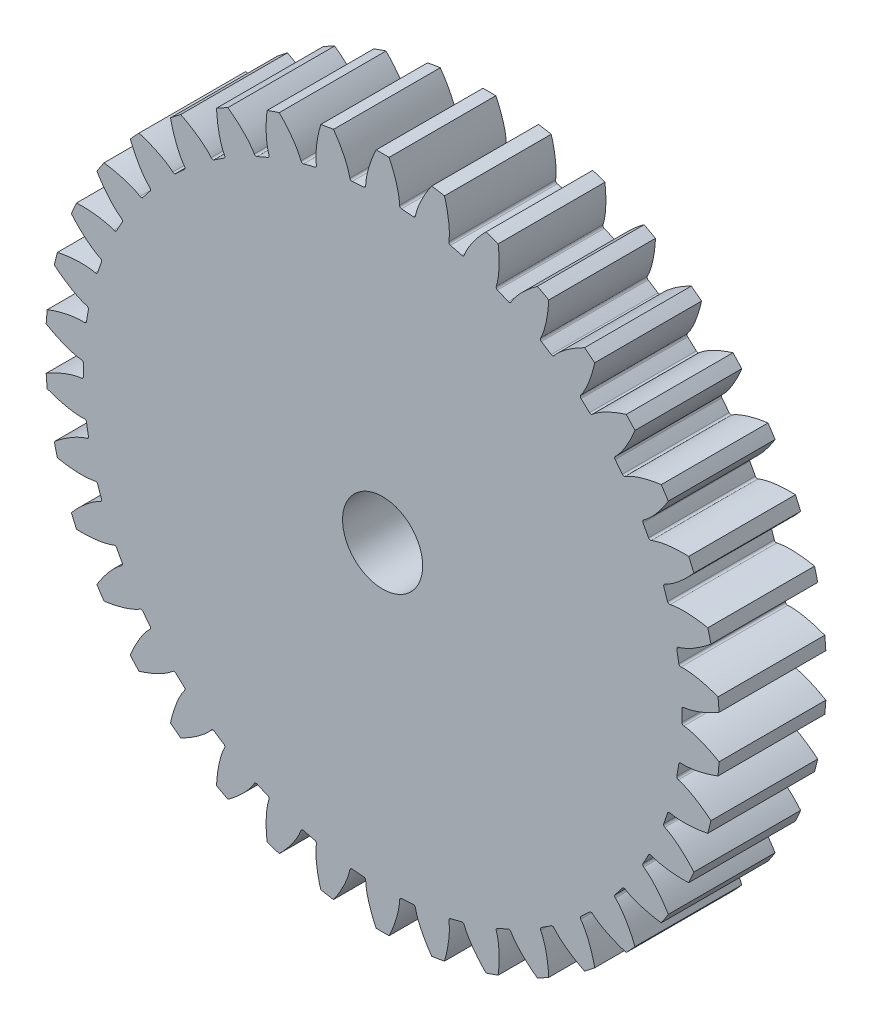
SolidWorks part; units mm, degrees
ref_plane "Front Plane" through (0, 0, 0) normal (0, 0, 1) x (1, 0, 0)
ref_plane "Top Plane" through (0, 0, 0) normal (0, 1, 0) x (1, 0, 0)
ref_plane "Right Plane" through (0, 0, 0) normal (1, 0, 0) x (0, 0, -1)
sketch "D" plane through (0, 0, 0) normal (0, 0, 1) x (1, 0, 0)
  circle A0 centre (0, 0) radius 12 construction
  dimension "D1" = 24
sketch "De, Di, Db" plane through (0, 0, 0) normal (0, 0, 1) x (1, 0, 0)
  circle A0 centre (0, 0) radius 11.2763 construction
  circle A1 centre (0, 0) radius 12.63 construction
  circle A2 centre (0, 0) radius 11.2125 construction
  point P7 (0, 0)
  dimension "D1" = 22.5526
  dimension "D2" = 25.26
  dimension "D3" = 22.425
sketch "Sketch4" plane through (0, 0, 0) normal (0, 0, 1) x (1, 0, 0)
  circle A0 centre (0, 0) radius 12.63 construction
  circle A1 centre (0, 0) radius 12.63
extrude "Addendum Extruded" add sketch "Sketch4" along normal mid plane 4
sketch "Tooth Profile Curve" plane through (0, 0, 0) normal (0, 0, 1) x (1, 0, 0)
  line L0 (0, 0) -> (12.63, 0) construction
  line L1 (0, 0) -> (11.2724, 0.2976) construction
  line L2 (0, 0) -> (11.9898, 0.4947) construction
  line L3 (11.2724, 0.2976) -> (11.2086, 0.296)
  line L4 (11.2125, 0) -> (12.63, 0)
  circle A0 centre (0, 0) radius 11.2763 construction
  circle A1 centre (0, 0) radius 12.63 construction
  circle A2 centre (0, 0) radius 11.2125 construction
  circle A3 centre (0, 0) radius 12 construction
  arc A4 (11.2086, 0.296) -> (11.2125, 0) centre (0, 0) cw
  arc A5 (12.63, 0) -> (12.6045, 0.8018) centre (0, 0) ccw
  spline S0 degree 4 poles (11.2724, 0.2976) (11.2807, 0.298) (11.304, 0.2997) (11.348, 0.3049) (11.4193, 0.3165) (11.5096, 0.3357) (11.6252, 0.3656) (11.76, 0.4073) (11.9063, 0.4598) (12.0633, 0.5241) (12.2177, 0.5945) (12.3696, 0.6705) (12.5188, 0.7513) (12.6969, 0.8551) (12.9066, 0.9878) (13.1456, 1.1546) (13.4091, 1.3574) (13.669, 1.578) (13.9172, 1.8065) (14.159, 2.0499) (14.3863, 2.2942) (14.6124, 2.5601) (14.8161, 2.8118) (15.0324, 3.1066) (15.2037, 3.3482) (15.4165, 3.6798) (15.5382, 3.8794) (15.676, 4.1173) (15.7347, 4.2251) (15.7709, 4.2915) knots 0 0 0 0 0 0.005377 0.015084 0.028532 0.04661 0.064855 0.092111 0.119476 0.146842 0.174209 0.201575 0.228941 0.256307 0.307035 0.361767 0.4165 0.471232 0.525964 0.580697 0.635429 0.690161 0.744894 0.799626 0.854358 0.909091 0.954545 1 1 1 1 1 construction
  spline S1 degree 4 poles (11.2724, 0.2976) (11.2807, 0.298) (11.304, 0.2997) (11.348, 0.3049) (11.4193, 0.3165) (11.5096, 0.3357) (11.6252, 0.3656) (11.76, 0.4073) (11.9063, 0.4598) (12.0633, 0.5241) (12.2177, 0.5945) (12.3696, 0.6705) (12.5188, 0.7513) (12.6969, 0.8551) (12.9066, 0.9878) (13.1456, 1.1546) (13.4091, 1.3574) (13.669, 1.578) (13.9172, 1.8065) (14.159, 2.0499) (14.3863, 2.2942) (14.6124, 2.5601) (14.8161, 2.8118) (15.0324, 3.1066) (15.2037, 3.3482) (15.3703, 3.6079) (15.4499, 3.7358) (15.4899, 3.8017) knots 0 0 0 0 0 0.005377 0.015084 0.028532 0.04661 0.064855 0.092111 0.119476 0.146842 0.174209 0.201575 0.228941 0.256307 0.307035 0.361767 0.4165 0.471232 0.525964 0.580697 0.635429 0.690161 0.744894 0.799626 0.854358 0.909091 0.909091 0.909091 0.909091 0.909091
  dimension "D1" = 2.363
  dimension "D2" = 0.85
  dimension "D3" = 1.513
extrude "1/2 Tooth Cut" cut sketch "Tooth Profile Curve" against normal mid plane 4
ref_plane "Plane of Mirroring" through (0, 0, 0) normal (0, 1, 0) x (1, 0, 0)
mirror "Mirror Tooth Cut" about plane through (0, 0, 0) normal (0, 1, 0) of "1/2 Tooth Cut"
fillet "Roots Fillet" radius 0.0788 2 edges at (11.2086, -0.296, 0) (11.2086, 0.296, 0)
pattern_circular "Circular Pattern of Teeth" count 38 over 360 about axis through (0, 0, -2) along (0, 0, 1) of "Mirror Tooth Cut", "1/2 Tooth Cut", "Roots Fillet"
sketch "Sketch5" plane through (0, 0, 0) normal (0, 0, 1) x (1, 0, 0)
  line L0 (1, 4) -> (-1, 4) construction
  line L1 (-1, 5) -> (1, 5)
  line L2 (-1, 5) -> (-1, 3.873)
  line L5 (1, 4) -> (1, 5)
  line L6 (1, 4) -> (1, 3.873)
  arc A0 (-1, 3.873) -> (1, 3.873) centre (0, 0) ccw
  circle A1 centre (0, 0) radius 4 construction
  point P9 (0, 5)
  dimension "D1" = 8
  dimension "D2" = 1
  dimension "D3" = 2
sketch "Sketch6" [suppressed] plane through (0, 0, 0) normal (0, 0, 1) x (1, 0, 0)
  line L6 (41.8591, 5.9947) -> (34.5048, 4.9415) construction
  line L7 (37.3883, 19.7543) -> (30.8195, 16.2837) construction
  line L8 (41.8591, 5.9947) -> (34.5048, 4.9415)
  line L9 (37.3883, 19.7543) -> (30.8195, 16.2837)
  arc A14 (52.1159, 14.1398) -> (50.4738, 19.1936) centre (0, 0) ccw construction
  arc A20 (34.5048, 4.9415) -> (33.5461, 3.7044) centre (34.6643, 3.8278) ccw construction
  arc A29 (29.3167, 16.721) -> (30.8195, 16.2837) centre (30.294, 17.2784) ccw construction
  circle A30 centre (0, 0) radius 33.75 construction
  arc A31 (52.1159, 14.1398) -> (50.4738, 19.1936) centre (0, 0) ccw
  arc A32 (34.5048, 4.9415) -> (33.5461, 3.7044) centre (34.6643, 3.8278) ccw
  arc A33 (29.3167, 16.721) -> (30.8195, 16.2837) centre (30.294, 17.2784) ccw
  arc A34 (29.3167, 16.721) -> (33.5461, 3.7044) centre (0, 0) ccw
  spline S2 degree 4 poles (965.1968, -1751.9554) (49.5722, -17.509) (34.0199, 17.1415) (35.6787, 19.1473) (37.9033, 19.963) (38.3849, 20.1134) (39.1305, 20.2925) (39.9677, 20.4275) (40.8649, 20.5145) (41.6597, 20.5534) (42.2962, 20.5635) (43.0686, 20.5519) (43.9989, 20.5031) (45.0849, 20.3985) (46.322, 20.2188) (47.5725, 19.978) (64.8653, 15.8708) (78.7396, -0.7897) (70.5074, -3.2513) (1756.2094, -1025.0114) knots -0.360808 -0.360808 -0.360808 -0.360808 -0.360808 0.005377 0.015084 0.028532 0.04661 0.092111 0.146842 0.174209 0.201575 0.228941 0.256307 0.307035 0.361767 0.4165 0.471232 0.525964 3.418372 3.418372 3.418372 3.418372 3.418372 only from (37.3883, 19.7543) to (50.4738, 19.1936) construction
  spline S3 degree 4 poles (-248.913, 1984.6901) (29.8132, 43.3029) (37.5982, 6.1286) (40.1192, 5.4809) (42.3983, 6.1286) (42.8764, 6.29) (43.5848, 6.5834) (44.3415, 6.9662) (45.1185, 7.4233) (45.7844, 7.859) (46.3053, 8.2249) (46.9233, 8.6882) (47.6473, 9.2745) (48.4644, 9.9975) (49.3596, 10.87) (50.2297, 11.7999) (61.8058, 25.2872) (63.2375, 46.9208) (55.1306, 44.0736) (818.3166, 1861.5256) knots -0.360808 -0.360808 -0.360808 -0.360808 -0.360808 0.005377 0.015084 0.028532 0.04661 0.092111 0.146842 0.174209 0.201575 0.228941 0.256307 0.307035 0.361767 0.4165 0.471232 0.525964 3.418372 3.418372 3.418372 3.418372 3.418372 only from (41.8591, 5.9947) to (52.1159, 14.1398) construction
  spline S4 degree 4 poles (37.3883, 19.7543) (37.4162, 19.7684) (37.4955, 19.8059) (37.6488, 19.8697) (37.9033, 19.963) (38.3849, 20.1134) (39.1305, 20.2925) (39.9677, 20.4275) (40.8649, 20.5145) (41.6597, 20.5534) (42.2962, 20.5635) (43.0686, 20.5519) (43.9989, 20.5031) (45.0849, 20.3985) (46.322, 20.2188) (47.5725, 19.978) (48.7682, 19.694) (49.6459, 19.4492) (50.2125, 19.2764) (50.4738, 19.1936) knots 0 0 0 0 0 0.005377 0.015084 0.028532 0.04661 0.092111 0.146842 0.174209 0.201575 0.228941 0.256307 0.307035 0.361767 0.4165 0.471232 0.525964 0.573123 0.573123 0.573123 0.573123 0.573123
  spline S5 degree 4 poles (41.8591, 5.9947) (41.8899, 5.9998) (41.9761, 6.016) (42.1376, 6.0545) (42.3983, 6.1286) (42.8764, 6.29) (43.5848, 6.5834) (44.3415, 6.9662) (45.1185, 7.4233) (45.7844, 7.859) (46.3053, 8.2249) (46.9233, 8.6882) (47.6473, 9.2745) (48.4644, 9.9975) (49.3596, 10.87) (50.2297, 11.7999) (51.0302, 12.7325) (51.5963, 13.4464) (51.9531, 13.9192) (52.1159, 14.1398) knots 0 0 0 0 0 0.005377 0.015084 0.028532 0.04661 0.092111 0.146842 0.174209 0.201575 0.228941 0.256307 0.307035 0.361767 0.4165 0.471232 0.525964 0.573123 0.573123 0.573123 0.573123 0.573123
extrude "Teeth Removing" [suppressed] cut sketch "Sketch6" against normal through all both flip side to cut
sketch "Sketch7" [suppressed] plane through (0, 0, 0) normal (0, 0, 1) x (1, 0, 0)
  line L0 (-3, 10) -> (3, 10)
  line L1 (3, 10) -> (3, 7.4162)
  line L2 (-3, 10) -> (-3, 7.4162)
  arc A0 (-3, 7.4162) -> (3, 7.4162) centre (0, 0) ccw
  point P1 (0, 10)
  dimension "D1" = 8
  dimension "D2" = 10
  dimension "D3" = 6
extrude "Cut-Extrude1" [suppressed] cut sketch "Sketch7" against normal through all both and the other way through all
sketch "Sketch8" [suppressed] plane through (0, 0, 0) normal (0, 0, 1) x (1, 0, 0)
  line L0 (-4.8226, 27.7752) -> (-3.9753, 22.8953) construction
  line L1 (4.8226, 27.7752) -> (3.9753, 22.8953) construction
  line L2 (-4.8226, 27.7752) -> (-3.9753, 22.8953)
  line L3 (4.8226, 27.7752) -> (3.9753, 22.8953)
  arc A0 (-4.5622, 22.0326) -> (4.5622, 22.0326) centre (0, 0) ccw
  arc A1 (-4.5622, 22.0326) -> (-3.9753, 22.8953) centre (-4.7142, 22.767) ccw construction
  arc A2 (3.9753, 22.8953) -> (4.5622, 22.0326) centre (4.7142, 22.767) ccw construction
  arc A3 (-4.5622, 22.0326) -> (-3.9753, 22.8953) centre (-4.7142, 22.767) ccw
  arc A4 (3.9753, 22.8953) -> (4.5622, 22.0326) centre (4.7142, 22.767) ccw
  arc A5 (-1.7713, 35.9564) -> (1.7713, 35.9564) centre (0, 0) cw
  spline S0 degree 4 poles (-2951.1447, 536.0596) (-42.0553, 30.3098) (3.4186, 24.472) (4.7778, 26.2412) (4.8488, 28.1447) (4.8449, 28.481) (4.8049, 28.9907) (4.718, 29.5493) (4.5883, 30.1361) (4.4492, 30.6481) (4.3245, 31.0537) (4.1581, 31.541) (3.9355, 32.1209) (3.6454, 32.7879) (3.2766, 33.5352) (2.8663, 34.2784) (-4.9345, 47.0779) (-24.4948, 52.3174) (-14.1166, 37.6796) (-2283.6828, 1979.2083) knots -0.444693 -0.444693 -0.444693 -0.444693 -0.444693 0.005377 0.015084 0.028532 0.04661 0.092111 0.146842 0.174209 0.201575 0.228941 0.256307 0.307035 0.361767 0.4165 0.471232 0.525964 4.228351 4.228351 4.228351 4.228351 4.228351 only from (4.8226, 27.7752) to (1.7713, 35.9564) construction
  spline S1 degree 4 poles (2951.1447, 536.0596) (42.0553, 30.3098) (-3.4186, 24.472) (-4.7778, 26.2412) (-4.8488, 28.1447) (-4.8449, 28.481) (-4.8049, 28.9907) (-4.718, 29.5493) (-4.5883, 30.1361) (-4.4492, 30.6481) (-4.3245, 31.0537) (-4.1581, 31.541) (-3.9355, 32.1209) (-3.6454, 32.7879) (-3.2766, 33.5352) (-2.8663, 34.2784) (4.9345, 47.0779) (24.4948, 52.3174) (14.1166, 37.6796) (2283.6828, 1979.2083) knots -0.444693 -0.444693 -0.444693 -0.444693 -0.444693 0.005377 0.015084 0.028532 0.04661 0.092111 0.146842 0.174209 0.201575 0.228941 0.256307 0.307035 0.361767 0.4165 0.471232 0.525964 4.228351 4.228351 4.228351 4.228351 4.228351 only from (-4.8226, 27.7752) to (-1.7713, 35.9564) construction
  spline S2 degree 4 poles (4.8226, 27.7752) (4.8257, 27.7958) (4.8332, 27.8538) (4.842, 27.9641) (4.8488, 28.1447) (4.8449, 28.481) (4.8049, 28.9907) (4.718, 29.5493) (4.5883, 30.1361) (4.4492, 30.6481) (4.3245, 31.0537) (4.1581, 31.541) (3.9355, 32.1209) (3.6454, 32.7879) (3.2766, 33.5352) (2.8663, 34.2784) (2.4399, 34.9781) (2.1039, 35.4841) (1.8776, 35.8078) (1.7713, 35.9564) knots 0 0 0 0 0 0.005377 0.015084 0.028532 0.04661 0.092111 0.146842 0.174209 0.201575 0.228941 0.256307 0.307035 0.361767 0.4165 0.471232 0.525964 0.573122 0.573122 0.573122 0.573122 0.573122
  spline S3 degree 4 poles (-4.8226, 27.7752) (-4.8257, 27.7958) (-4.8332, 27.8538) (-4.842, 27.9641) (-4.8488, 28.1447) (-4.8449, 28.481) (-4.8049, 28.9907) (-4.718, 29.5493) (-4.5883, 30.1361) (-4.4492, 30.6481) (-4.3245, 31.0537) (-4.1581, 31.541) (-3.9355, 32.1209) (-3.6454, 32.7879) (-3.2766, 33.5352) (-2.8663, 34.2784) (-2.4399, 34.9781) (-2.1039, 35.4841) (-1.8776, 35.8078) (-1.7713, 35.9564) knots 0 0 0 0 0 0.005377 0.015084 0.028532 0.04661 0.092111 0.146842 0.174209 0.201575 0.228941 0.256307 0.307035 0.361767 0.4165 0.471232 0.525964 0.573122 0.573122 0.573122 0.573122 0.573122
extrude "Cut-Extrude2" [suppressed] cut sketch "Sketch8" against normal through all both and the other way through all flip side to cut
sketch "Sketch9" [suppressed] plane through (0, 0, 0) normal (0, 0, 1) x (1, 0, 0)
  circle A0 centre (0, 0) radius 4
  dimension "D1" = 8
extrude "Cut-Extrude3" [suppressed] cut sketch "Sketch9" against normal through all both and the other way through all
sketch "Sketch10" [suppressed] plane through (0, 0, 0) normal (0, 0, 1) x (1, 0, 0)
  circle A0 centre (0, 0) radius 6
  dimension "D1" = 12
extrude "Cut-Extrude4" [suppressed] cut sketch "Sketch10" against normal through all both and the other way through all
sketch "Sketch11" [suppressed] plane through (0, 0, 0) normal (0, 0, 1) x (1, 0, 0)
  line L0 (27.9061, 3.9965) -> (23.0032, 3.2943) construction
  line L1 (24.9255, 13.1696) -> (20.5463, 10.8558) construction
  line L2 (-4.8226, 27.7752) -> (-3.9753, 22.8953) construction
  line L3 (4.8226, 27.7752) -> (3.9753, 22.8953) construction
  line L4 (27.9061, 3.9965) -> (23.0032, 3.2943)
  line L5 (24.9255, 13.1696) -> (20.5463, 10.8558)
  line L6 (-4.8226, 27.7752) -> (-3.9753, 22.8953)
  line L7 (4.8226, 27.7752) -> (3.9753, 22.8953)
  arc A0 (-4.5622, 22.0326) -> (22.3641, 2.4696) centre (0, 0) ccw
  arc A1 (19.5445, 11.1473) -> (20.5463, 10.8558) centre (20.196, 11.5189) ccw construction
  arc A2 (23.0032, 3.2943) -> (22.3641, 2.4696) centre (23.1095, 2.5519) ccw construction
  arc A4 (3.9753, 22.8953) -> (4.5622, 22.0326) centre (4.7142, 22.767) ccw construction
  arc A5 (19.5445, 11.1473) -> (20.5463, 10.8558) centre (20.196, 11.5189) ccw
  arc A6 (23.0032, 3.2943) -> (22.3641, 2.4696) centre (23.1095, 2.5519) ccw
  arc A7 (-4.5622, 22.0326) -> (-3.9753, 22.8953) centre (-4.7142, 22.767) ccw construction
  arc A8 (3.9753, 22.8953) -> (4.5622, 22.0326) centre (4.7142, 22.767) ccw
  arc A9 (19.5445, 11.1473) -> (4.5622, 22.0326) centre (0, 0) ccw
  arc A10 (-1.7713, 35.9564) -> (1.7713, 35.9564) centre (0, 0) cw
  arc A11 (33.6492, 12.7957) -> (34.7439, 9.4265) centre (0, 0) cw
  arc A12 (-4.5622, 22.0326) -> (-3.9753, 22.8953) centre (-4.7142, 22.767) ccw
  spline S0 degree 4 poles (-402.1308, 2972.3569) (15.8305, 49.3632) (24.3306, 4.311) (26.4333, 3.565) (28.2656, 4.0857) (28.5842, 4.1933) (29.0566, 4.3889) (29.561, 4.6441) (30.079, 4.9488) (30.5229, 5.2393) (30.8702, 5.4833) (31.2822, 5.7922) (31.7649, 6.183) (32.3096, 6.665) (32.9064, 7.2467) (33.4865, 7.8666) (43.2489, 19.2409) (42.1875, 39.4629) (31.4732, 25.0693) (1176.6422, 2783.5204) knots -0.444693 -0.444693 -0.444693 -0.444693 -0.444693 0.005377 0.015084 0.028532 0.04661 0.092111 0.146842 0.174209 0.201575 0.228941 0.256307 0.307035 0.361767 0.4165 0.471232 0.525964 4.228351 4.228351 4.228351 4.228351 4.228351 only from (27.9061, 3.9965) to (34.7439, 9.4265) construction
  spline S1 degree 4 poles (1421.7769, -2641.0538) (41.8221, -30.6307) (22.2178, 10.8135) (23.4804, 12.6529) (25.2689, 13.3086) (25.5899, 13.4089) (26.087, 13.5283) (26.6451, 13.6183) (27.2433, 13.6763) (27.7732, 13.7022) (28.1975, 13.709) (28.7124, 13.7013) (29.3326, 13.6688) (30.0566, 13.599) (30.8813, 13.4792) (31.715, 13.3187) (46.2986, 9.8549) (57.3261, -7.129) (40.1977, -1.782) (2588.0358, -1560.3024) knots -0.444693 -0.444693 -0.444693 -0.444693 -0.444693 0.005377 0.015084 0.028532 0.04661 0.092111 0.146842 0.174209 0.201575 0.228941 0.256307 0.307035 0.361767 0.4165 0.471232 0.525964 4.228351 4.228351 4.228351 4.228351 4.228351 only from (24.9255, 13.1696) to (33.6492, 12.7957) construction
  spline S2 degree 4 poles (2951.1447, 536.0596) (42.0553, 30.3098) (-3.4186, 24.472) (-4.7778, 26.2412) (-4.8488, 28.1447) (-4.8449, 28.481) (-4.8049, 28.9907) (-4.718, 29.5493) (-4.5883, 30.1361) (-4.4492, 30.6481) (-4.3245, 31.0537) (-4.1581, 31.541) (-3.9355, 32.1209) (-3.6454, 32.7879) (-3.2766, 33.5352) (-2.8663, 34.2784) (4.9345, 47.0779) (24.4948, 52.3174) (14.1166, 37.6796) (2283.6828, 1979.2083) knots -0.444693 -0.444693 -0.444693 -0.444693 -0.444693 0.005377 0.015084 0.028532 0.04661 0.092111 0.146842 0.174209 0.201575 0.228941 0.256307 0.307035 0.361767 0.4165 0.471232 0.525964 4.228351 4.228351 4.228351 4.228351 4.228351 only from (-4.8226, 27.7752) to (-1.7713, 35.9564) construction
  spline S3 degree 4 poles (-2951.1447, 536.0596) (-42.0553, 30.3098) (3.4186, 24.472) (4.7778, 26.2412) (4.8488, 28.1447) (4.8449, 28.481) (4.8049, 28.9907) (4.718, 29.5493) (4.5883, 30.1361) (4.4492, 30.6481) (4.3245, 31.0537) (4.1581, 31.541) (3.9355, 32.1209) (3.6454, 32.7879) (3.2766, 33.5352) (2.8663, 34.2784) (-4.9345, 47.0779) (-24.4948, 52.3174) (-14.1166, 37.6796) (-2283.6828, 1979.2083) knots -0.444693 -0.444693 -0.444693 -0.444693 -0.444693 0.005377 0.015084 0.028532 0.04661 0.092111 0.146842 0.174209 0.201575 0.228941 0.256307 0.307035 0.361767 0.4165 0.471232 0.525964 4.228351 4.228351 4.228351 4.228351 4.228351 only from (4.8226, 27.7752) to (1.7713, 35.9564) construction
  spline S4 degree 4 poles (27.9061, 3.9965) (27.9266, 3.9998) (27.9841, 4.0106) (28.0917, 4.0363) (28.2656, 4.0857) (28.5842, 4.1933) (29.0566, 4.3889) (29.561, 4.6441) (30.079, 4.9488) (30.5229, 5.2393) (30.8702, 5.4833) (31.2822, 5.7922) (31.7649, 6.183) (32.3096, 6.665) (32.9064, 7.2467) (33.4865, 7.8666) (34.0201, 8.4883) (34.3975, 8.9643) (34.6354, 9.2795) (34.7439, 9.4265) knots 0 0 0 0 0 0.005377 0.015084 0.028532 0.04661 0.092111 0.146842 0.174209 0.201575 0.228941 0.256307 0.307035 0.361767 0.4165 0.471232 0.525964 0.573122 0.573122 0.573122 0.573122 0.573122
  spline S5 degree 4 poles (24.9255, 13.1696) (24.9442, 13.1789) (24.997, 13.204) (25.0992, 13.2464) (25.2689, 13.3086) (25.5899, 13.4089) (26.087, 13.5283) (26.6451, 13.6183) (27.2433, 13.6763) (27.7732, 13.7022) (28.1975, 13.709) (28.7124, 13.7013) (29.3326, 13.6688) (30.0566, 13.599) (30.8813, 13.4792) (31.715, 13.3187) (32.5122, 13.1293) (33.0972, 12.9661) (33.475, 12.8509) (33.6492, 12.7957) knots 0 0 0 0 0 0.005377 0.015084 0.028532 0.04661 0.092111 0.146842 0.174209 0.201575 0.228941 0.256307 0.307035 0.361767 0.4165 0.471232 0.525964 0.573122 0.573122 0.573122 0.573122 0.573122
  spline S6 degree 4 poles (-4.8226, 27.7752) (-4.8257, 27.7958) (-4.8332, 27.8538) (-4.842, 27.9641) (-4.8488, 28.1447) (-4.8449, 28.481) (-4.8049, 28.9907) (-4.718, 29.5493) (-4.5883, 30.1361) (-4.4492, 30.6481) (-4.3245, 31.0537) (-4.1581, 31.541) (-3.9355, 32.1209) (-3.6454, 32.7879) (-3.2766, 33.5352) (-2.8663, 34.2784) (-2.4399, 34.9781) (-2.1039, 35.4841) (-1.8776, 35.8078) (-1.7713, 35.9564) knots 0 0 0 0 0 0.005377 0.015084 0.028532 0.04661 0.092111 0.146842 0.174209 0.201575 0.228941 0.256307 0.307035 0.361767 0.4165 0.471232 0.525964 0.573122 0.573122 0.573122 0.573122 0.573122
  spline S7 degree 4 poles (4.8226, 27.7752) (4.8257, 27.7958) (4.8332, 27.8538) (4.842, 27.9641) (4.8488, 28.1447) (4.8449, 28.481) (4.8049, 28.9907) (4.718, 29.5493) (4.5883, 30.1361) (4.4492, 30.6481) (4.3245, 31.0537) (4.1581, 31.541) (3.9355, 32.1209) (3.6454, 32.7879) (3.2766, 33.5352) (2.8663, 34.2784) (2.4399, 34.9781) (2.1039, 35.4841) (1.8776, 35.8078) (1.7713, 35.9564) knots 0 0 0 0 0 0.005377 0.015084 0.028532 0.04661 0.092111 0.146842 0.174209 0.201575 0.228941 0.256307 0.307035 0.361767 0.4165 0.471232 0.525964 0.573122 0.573122 0.573122 0.573122 0.573122
extrude "Cut-Extrude6" [suppressed] cut sketch "Sketch11" against normal through all both and the other way through all flip side to cut
sketch "Sketch12" [suppressed] plane through (0, 0, 0) normal (0, 0, 1) x (1, 0, 0)
  line L0 (-20.2274, -19.636) -> (-16.6736, -16.1861) construction
  line L1 (-12.4243, -25.3053) -> (-10.2415, -20.8593) construction
  line L2 (4.8226, 27.7752) -> (3.9753, 22.8953) construction
  line L3 (-4.8226, 27.7752) -> (-3.9753, 22.8953) construction
  line L4 (-20.2274, -19.636) -> (-16.6736, -16.1861)
  line L5 (-12.4243, -25.3053) -> (-10.2415, -20.8593)
  line L6 (4.8226, 27.7752) -> (3.9753, 22.8953)
  line L7 (-4.8226, 27.7752) -> (-3.9753, 22.8953)
  arc A0 (-9.2596, -20.5063) -> (4.5622, 22.0326) centre (0, 0) ccw
  arc A1 (-9.2596, -20.5063) -> (-10.2415, -20.8593) centre (-9.5682, -21.1899) ccw construction
  arc A2 (-16.6736, -16.1861) -> (-16.6413, -15.1432) centre (-17.196, -15.648) ccw construction
  arc A3 (-4.5622, 22.0326) -> (-3.9753, 22.8953) centre (-4.7142, 22.767) ccw construction
  arc A4 (3.9753, 22.8953) -> (4.5622, 22.0326) centre (4.7142, 22.767) ccw construction
  arc A5 (-9.2596, -20.5063) -> (-10.2415, -20.8593) centre (-9.5682, -21.1899) ccw
  arc A6 (-16.6736, -16.1861) -> (-16.6413, -15.1432) centre (-17.196, -15.648) ccw
  arc A7 (-4.5622, 22.0326) -> (-3.9753, 22.8953) centre (-4.7142, 22.767) ccw
  arc A8 (3.9753, 22.8953) -> (4.5622, 22.0326) centre (4.7142, 22.767) ccw
  arc A9 (-4.5622, 22.0326) -> (-16.6413, -15.1432) centre (0, 0) ccw
  arc A10 (1.7713, 35.9564) -> (-1.7713, 35.9564) centre (0, 0) ccw
  arc A11 (-19.7016, -30.1305) -> (-22.5676, -28.0482) centre (0, 0) cw
  spline S0 degree 4 poles (2072.4383, -2168.3207) (16.2078, -49.2406) (-17.15, -17.7889) (-19.2895, -18.4213) (-20.4658, -19.9195) (-20.6604, -20.1939) (-20.9275, -20.6297) (-21.1856, -21.1327) (-21.4256, -21.6837) (-21.614, -22.1796) (-21.7515, -22.5811) (-21.9033, -23.0732) (-22.064, -23.6731) (-22.2214, -24.3832) (-22.3623, -25.2046) (-22.4673, -26.0471) (-23.6796, -40.9873) (-10.9347, -56.7234) (-10.727, -38.7809) (684.1887, -2943.5283) knots -0.444693 -0.444693 -0.444693 -0.444693 -0.444693 0.005377 0.015084 0.028532 0.04661 0.092111 0.146842 0.174209 0.201575 0.228941 0.256307 0.307035 0.361767 0.4165 0.471232 0.525964 4.228351 4.228351 4.228351 4.228351 4.228351 only from (-20.2274, -19.636) to (-22.5676, -28.0482) construction
  spline S1 degree 4 poles (-2702.6142, 1300.958) (-51.8391, 0.1983) (-11.6186, -21.8076) (-11.5589, -24.0379) (-12.6203, -25.6196) (-12.8211, -25.8894) (-13.1531, -26.2782) (-13.5517, -26.6791) (-14.0016, -27.0776) (-14.415, -27.41) (-14.7543, -27.6649) (-15.1754, -27.9613) (-15.6963, -28.2995) (-16.323, -28.6687) (-17.0606, -29.0565) (-17.8295, -29.4166) (-31.6638, -35.1864) (-50.5681, -27.928) (-33.5681, -22.1859) (-3010.8877, -258.8981) knots -0.444693 -0.444693 -0.444693 -0.444693 -0.444693 0.005377 0.015084 0.028532 0.04661 0.092111 0.146842 0.174209 0.201575 0.228941 0.256307 0.307035 0.361767 0.4165 0.471232 0.525964 4.228351 4.228351 4.228351 4.228351 4.228351 only from (-12.4243, -25.3053) to (-19.7016, -30.1305) construction
  spline S2 degree 4 poles (2951.1447, 536.0596) (42.0553, 30.3098) (-3.4186, 24.472) (-4.7778, 26.2412) (-4.8488, 28.1447) (-4.8449, 28.481) (-4.8049, 28.9907) (-4.718, 29.5493) (-4.5883, 30.1361) (-4.4492, 30.6481) (-4.3245, 31.0537) (-4.1581, 31.541) (-3.9355, 32.1209) (-3.6454, 32.7879) (-3.2766, 33.5352) (-2.8663, 34.2784) (4.9345, 47.0779) (24.4948, 52.3174) (14.1166, 37.6796) (2283.6828, 1979.2083) knots -0.444693 -0.444693 -0.444693 -0.444693 -0.444693 0.005377 0.015084 0.028532 0.04661 0.092111 0.146842 0.174209 0.201575 0.228941 0.256307 0.307035 0.361767 0.4165 0.471232 0.525964 4.228351 4.228351 4.228351 4.228351 4.228351 only from (-4.8226, 27.7752) to (-1.7713, 35.9564) construction
  spline S3 degree 4 poles (-2951.1447, 536.0596) (-42.0553, 30.3098) (3.4186, 24.472) (4.7778, 26.2412) (4.8488, 28.1447) (4.8449, 28.481) (4.8049, 28.9907) (4.718, 29.5493) (4.5883, 30.1361) (4.4492, 30.6481) (4.3245, 31.0537) (4.1581, 31.541) (3.9355, 32.1209) (3.6454, 32.7879) (3.2766, 33.5352) (2.8663, 34.2784) (-4.9345, 47.0779) (-24.4948, 52.3174) (-14.1166, 37.6796) (-2283.6828, 1979.2083) knots -0.444693 -0.444693 -0.444693 -0.444693 -0.444693 0.005377 0.015084 0.028532 0.04661 0.092111 0.146842 0.174209 0.201575 0.228941 0.256307 0.307035 0.361767 0.4165 0.471232 0.525964 4.228351 4.228351 4.228351 4.228351 4.228351 only from (4.8226, 27.7752) to (1.7713, 35.9564) construction
  spline S4 degree 4 poles (-20.2274, -19.636) (-20.2421, -19.6508) (-20.2822, -19.6933) (-20.3542, -19.7774) (-20.4658, -19.9195) (-20.6604, -20.1939) (-20.9275, -20.6297) (-21.1856, -21.1327) (-21.4256, -21.6837) (-21.614, -22.1796) (-21.7515, -22.5811) (-21.9033, -23.0732) (-22.064, -23.6731) (-22.2214, -24.3832) (-22.3623, -25.2046) (-22.4673, -26.0471) (-22.5335, -26.8637) (-22.5591, -27.4706) (-22.5663, -27.8654) (-22.5676, -28.0482) knots 0 0 0 0 0 0.005377 0.015084 0.028532 0.04661 0.092111 0.146842 0.174209 0.201575 0.228941 0.256307 0.307035 0.361767 0.4165 0.471232 0.525964 0.573122 0.573122 0.573122 0.573122 0.573122
  spline S5 degree 4 poles (-12.4243, -25.3053) (-12.4339, -25.3238) (-12.4619, -25.3751) (-12.5196, -25.4695) (-12.6203, -25.6196) (-12.8211, -25.8894) (-13.1531, -26.2782) (-13.5517, -26.6791) (-14.0016, -27.0776) (-14.415, -27.41) (-14.7543, -27.6649) (-15.1754, -27.9613) (-15.6963, -28.2995) (-16.323, -28.6687) (-17.0606, -29.0565) (-17.8295, -29.4166) (-18.5857, -29.732) (-19.1549, -29.9439) (-19.5282, -30.0727) (-19.7016, -30.1305) knots 0 0 0 0 0 0.005377 0.015084 0.028532 0.04661 0.092111 0.146842 0.174209 0.201575 0.228941 0.256307 0.307035 0.361767 0.4165 0.471232 0.525964 0.573122 0.573122 0.573122 0.573122 0.573122
  spline S6 degree 4 poles (-4.8226, 27.7752) (-4.8257, 27.7958) (-4.8332, 27.8538) (-4.842, 27.9641) (-4.8488, 28.1447) (-4.8449, 28.481) (-4.8049, 28.9907) (-4.718, 29.5493) (-4.5883, 30.1361) (-4.4492, 30.6481) (-4.3245, 31.0537) (-4.1581, 31.541) (-3.9355, 32.1209) (-3.6454, 32.7879) (-3.2766, 33.5352) (-2.8663, 34.2784) (-2.4399, 34.9781) (-2.1039, 35.4841) (-1.8776, 35.8078) (-1.7713, 35.9564) knots 0 0 0 0 0 0.005377 0.015084 0.028532 0.04661 0.092111 0.146842 0.174209 0.201575 0.228941 0.256307 0.307035 0.361767 0.4165 0.471232 0.525964 0.573122 0.573122 0.573122 0.573122 0.573122
  spline S7 degree 4 poles (4.8226, 27.7752) (4.8257, 27.7958) (4.8332, 27.8538) (4.842, 27.9641) (4.8488, 28.1447) (4.8449, 28.481) (4.8049, 28.9907) (4.718, 29.5493) (4.5883, 30.1361) (4.4492, 30.6481) (4.3245, 31.0537) (4.1581, 31.541) (3.9355, 32.1209) (3.6454, 32.7879) (3.2766, 33.5352) (2.8663, 34.2784) (2.4399, 34.9781) (2.1039, 35.4841) (1.8776, 35.8078) (1.7713, 35.9564) knots 0 0 0 0 0 0.005377 0.015084 0.028532 0.04661 0.092111 0.146842 0.174209 0.201575 0.228941 0.256307 0.307035 0.361767 0.4165 0.471232 0.525964 0.573122 0.573122 0.573122 0.573122 0.573122
extrude "Cut-Extrude7" [suppressed] cut sketch "Sketch12" against normal through all both and the other way through all flip side to cut
sketch "Sketch13" plane through (0, 0, 2) normal (0, 0, 1) x (1, 0, 0)
  circle A0 centre (0, 0) radius 1.5
  dimension "D1" = 3
extrude "Cut-Extrude8" cut sketch "Sketch13" against normal through all
equation "\"D\"= \"D1@D\"'Pitch Diameter"
equation "\"m\"= .63'Module"
equation "\"z\"= \"D\" / \"m\"'Numer of Teeth"
equation "\"De\"= \"m\" * ( \"z\" + 2 )'Addendeum Diameter"
equation "\"Di\"= \"m\" * ( \"z\" - 2.5 )'Dedendum Diameter"
equation "\"Phi\"= 20'Pressure Angle"
equation "\"Db\"= \"D\" * cos ( \"Phi\" )'Base Diameter"
equation "\"k\"= \"m\"'Factor k"
equation "\"f\"= 1.25 * \"m\"'Factor f"
equation "\"Rf\"= ( \"f\" - \"k\" ) / 2'Roots Fillet"
equation "\"D1@De, Di, Db\"=\"Db\""
equation "\"D2@De, Di, Db\"=\"De\""
equation "\"D3@De, Di, Db\"=\"Di\""
equation "\"D1@Circular Pattern of Teeth\"=\"z\""
equation "\"D1@Roots Fillet\"=\"Rf\""
equation "\"Teta1\"= 360 / ( 4 * \"z\" )'Angle 1 For Tooth Cut"
equation "\"D1@Tooth Profile Curve\"=\"Teta1\""
equation "\"D3@Tooth Profile Curve\"=\"Teta1\"-\"D2@Tooth Profile Curve\""
equation "\"D1\" = \"Rf\""
